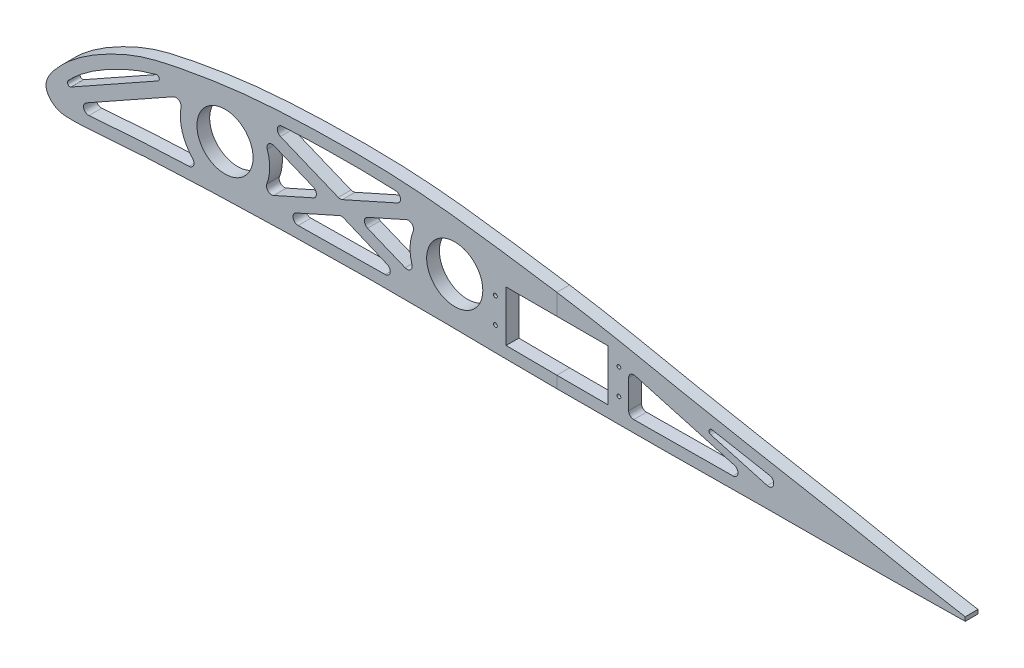
SolidWorks part; units mm, degrees
ref_plane "Front Plane" through (0, 0, 0) normal (0, 0, 1) x (1, 0, 0)
ref_plane "Top Plane" through (0, 0, 0) normal (0, 1, 0) x (1, 0, 0)
ref_plane "Right Plane" through (0, 0, 0) normal (1, 0, 0) x (0, 0, -1)
curve "Curve2"
  spline degree 3 poles (360, 0.774, 0) (353.9747, 1.7923, 0) (341.8992, 3.833, 0) (317.929, 8.8515, 0) (287.8005, 14.3115, 0) (251.6459, 20.8994, 0) (215.7742, 28.6405, 0) (179.6243, 33.9497, 0) (143.6184, 38.7406, 0) (107.4505, 38.9574, 0) (77.3391, 37.3603, 0) (53.4361, 33.3953, 0) (38.2175, 30.219, 0) (26.4469, 25.0774, 0) (17.386, 20.225, 0) (9.7945, 14.7499, 0) (3.5415, 8.6051, 0) (-2.4818, 0.9357, 0) (3.758, -5.4139, 0) (10.5774, -5.7626, 0) (18.0806, -5.3806, 0) (27.0623, -4.6056, 0) (39.0449, -3.7653, 0) (54.0396, -3.0817, 0) (78.026, -2.1616, 0) (108.0193, -1.4806, 0) (144.023, -1.1541, 0) (180.0214, -1.8085, 0) (216.0253, -1.9147, 0) (252.0235, -1.7429, 0) (288.0192, -1.2657, 0) (318.0184, -1.4154, 0) (342.0107, -1.0116, 0) (354.0048, -0.8532, 0) (360, -0.774, 0) knots 0 0 0 0 0.02483 0.049761 0.099505 0.149249 0.199104 0.24856 0.297718 0.346503 0.395331 0.419969 0.445008 0.458171 0.47196 0.48692 0.495371 0.509218 0.518335 0.524512 0.536705 0.548918 0.561125 0.585522 0.609907 0.65867 0.70743 0.756207 0.804971 0.853736 0.902492 0.951256 0.975635 1 1 1 1
sketch "Sketch1" plane through (0, 0, 0) normal (0, 0, 1) x (1, 0, 0)
  line L0 (360, 0.774) -> (360, -0.774)
  spline S0 degree 3 poles (460.5954, -1977.8862) (673.5327, 25.178) (493.5092, -27.9082) (317.929, 8.8515) (287.8005, 14.3115) (251.6459, 20.8994) (215.7742, 28.6405) (179.6243, 33.9497) (143.6184, 38.7406) (107.4505, 38.9574) (77.3391, 37.3603) (53.4361, 33.3953) (38.2175, 30.219) (26.4469, 25.0774) (17.386, 20.225) (9.7945, 14.7499) (3.5415, 8.6051) (-2.4818, 0.9357) (3.758, -5.4139) (10.5774, -5.7626) (18.0806, -5.3806) (27.0623, -4.6056) (39.0449, -3.7653) (54.0396, -3.0817) (78.026, -2.1616) (108.0193, -1.4806) (144.023, -1.1541) (180.0214, -1.8085) (216.0253, -1.9147) (252.0235, -1.7429) (288.0192, -1.2657) (318.0184, -1.4154) (662.5746, 4.3841) (995.4005, -23.4398) (1308.3871, 1672.4433) knots -0.629362 -0.629362 -0.629362 -0.629362 0.02483 0.049761 0.099505 0.149249 0.199104 0.24856 0.297718 0.346503 0.395331 0.419969 0.445008 0.458171 0.47196 0.48692 0.495371 0.509218 0.518335 0.524512 0.536705 0.548918 0.561125 0.585522 0.609907 0.65867 0.70743 0.756207 0.804971 0.853736 0.902492 0.951256 0.975635 2.302817 2.302817 2.302817 2.302817 only from (360, 0.774) to (360, -0.774) construction
  spline S1 degree 3 poles (360, 0.774) (353.9747, 1.7923) (341.8992, 3.833) (317.929, 8.8515) (287.8005, 14.3115) (251.6459, 20.8994) (215.7742, 28.6405) (179.6243, 33.9497) (143.6184, 38.7406) (107.4505, 38.9574) (77.3391, 37.3603) (53.4361, 33.3953) (38.2175, 30.219) (26.4469, 25.0774) (17.386, 20.225) (9.7945, 14.7499) (3.5415, 8.6051) (-2.4818, 0.9357) (3.758, -5.4139) (10.5774, -5.7626) (18.0806, -5.3806) (27.0623, -4.6056) (39.0449, -3.7653) (54.0396, -3.0817) (78.026, -2.1616) (108.0193, -1.4806) (144.023, -1.1541) (180.0214, -1.8085) (216.0253, -1.9147) (252.0235, -1.7429) (288.0192, -1.2657) (318.0184, -1.4154) (342.0107, -1.0116) (354.0048, -0.8532) (360, -0.774) knots 0 0 0 0 0.02483 0.049761 0.099505 0.149249 0.199104 0.24856 0.297718 0.346503 0.395331 0.419969 0.445008 0.458171 0.47196 0.48692 0.495371 0.509218 0.518335 0.524512 0.536705 0.548918 0.561125 0.585522 0.609907 0.65867 0.70743 0.756207 0.804971 0.853736 0.902492 0.951256 0.975635 1 1 1 1
extrude "Boss-Extrude1" add sketch "Sketch1" along normal blind 5
sketch "Sketch3" plane through (0, 0, 5) normal (0, 0, 1) x (1, 0, 0)
  line L0 (284.1512, 10.3055) -> (284.9744, 10.1558)
  line L3 (285, -1.3899) -> (284.9744, 3.21) construction
  line L4 (284.9744, 10.1558) -> (284.9744, 14.8312) construction
  line L5 (284.9744, 3.21) -> (284.9744, 10.1558)
  spline S0 degree 3 poles (344.1847, -2970.9307) (723.5062, 41.4838) (516.074, -32.6324) (317.929, 8.8515) (287.8005, 14.3115) (251.6459, 20.8994) (215.7742, 28.6405) (179.6243, 33.9497) (143.6184, 38.7406) (107.4505, 38.9574) (77.3391, 37.3603) (53.4361, 33.3953) (38.2175, 30.219) (26.4469, 25.0774) (17.386, 20.225) (9.7945, 14.7499) (3.5415, 8.6051) (-2.4818, 0.9357) (3.758, -5.4139) (10.5774, -5.7626) (18.0806, -5.3806) (27.0623, -4.6056) (39.0449, -3.7653) (54.0396, -3.0817) (78.026, -2.1616) (108.0193, -1.4806) (144.023, -1.1541) (180.0214, -1.8085) (216.0253, -1.9147) (252.0235, -1.7429) (288.0192, -1.2657) (318.0184, -1.4154) (716.4553, 5.2911) (1103.2559, -33.3331) (1462.1178, 2660.5017) knots -0.723033 -0.723033 -0.723033 -0.723033 0.02483 0.049761 0.099505 0.149249 0.199104 0.24856 0.297718 0.346503 0.395331 0.419969 0.445008 0.458171 0.47196 0.48692 0.495371 0.509218 0.518335 0.524512 0.536705 0.548918 0.561125 0.585522 0.609907 0.65867 0.70743 0.756207 0.804971 0.853736 0.902492 0.951256 0.975635 2.521796 2.521796 2.521796 2.521796 only from (360, 0.774) to (360, -0.774) construction
  spline S1 degree 3 poles (284.9744, 14.8312) (273.8733, 16.8505) (250.7091, 21.1015) (215.7742, 28.6405) (179.6243, 33.9497) (143.6184, 38.7406) (107.4505, 38.9574) (77.3391, 37.3603) (53.4361, 33.3953) (38.2175, 30.219) (26.4469, 25.0774) (17.386, 20.225) (9.7945, 14.7499) (3.5415, 8.6051) (-2.4818, 0.9357) (3.758, -5.4139) (10.5774, -5.7626) (18.0806, -5.3806) (27.0623, -4.6056) (39.0449, -3.7653) (54.0396, -3.0817) (78.026, -2.1616) (108.0193, -1.4806) (144.023, -1.1541) (180.0214, -1.8085) (216.0253, -1.9147) (251.0175, -1.7477) (274.0081, -1.4511) (285, -1.3899) knots 0.103398 0.103398 0.103398 0.103398 0.149249 0.199104 0.24856 0.297718 0.346503 0.395331 0.419969 0.445008 0.458171 0.47196 0.48692 0.495371 0.509218 0.518335 0.524512 0.536705 0.548918 0.561125 0.585522 0.609907 0.65867 0.70743 0.756207 0.804971 0.853736 0.898404 0.898404 0.898404 0.898404 construction
  spline S2 degree 1 poles (284.1512, 10.3055) (284.9744, 3.21) knots 0 0 1 1 construction
  spline S3 degree 3 poles (284.1512, 10.3055) (278.1277, 11.4011) (266.0952, 13.5977) (248.0033, 17.0941) (230.0297, 20.8366) (212.1625, 24.3023) (194.1819, 27.1662) (176.0385, 29.7488) (157.941, 32.1627) (139.9629, 33.7938) (121.8825, 34.2715) (103.6458, 33.9966) (88.5285, 33.2788) (76.5491, 32.181) (67.6356, 31.0449) (58.7258, 29.5821) (49.758, 27.9291) (42.5828, 26.2693) (37.1269, 24.5364) (33.1259, 22.9657) (29.1255, 21.1456) (25.1876, 19.172) (21.3948, 17.0517) (17.7124, 14.7189) (14.2021, 12.1748) (11.0304, 9.5132) (8.6387, 7.1256) (6.5778, 4.8171) (5.3253, 3.1689) (4.5747, 1.7655) (4.4647, 1.1378) (4.4812, 1.0445) (4.4784, 1.0061) (4.8205, 0.3506) (5.6085, -0.325) (6.2267, -0.6574) (6.7532, -0.8463) (7.8538, -1.0238) (10.0098, -1.0519) (12.1694, -1.0299) (14.3579, -0.9469) (16.5714, -0.8217) (19.5647, -0.6155) (23.3403, -0.3137) (27.9445, 0.059) (32.5568, 0.3895) (38.7092, 0.7806) (46.3902, 1.1764) (55.5744, 1.5696) (67.8164, 2.053) (83.1362, 2.5431) (107.6344, 3.0806) (132.1396, 3.3831) (156.6801, 3.1986) (175.0192, 2.9224) (193.3182, 2.7563) (217.7439, 2.7049) (242.175, 2.7972) (266.6035, 3.0568) (278.8536, 3.176) (284.9744, 3.21) knots 0.103398 0.103398 0.103398 0.103398 0.128242 0.153086 0.17793 0.202774 0.227618 0.252461 0.277305 0.302149 0.326993 0.351837 0.376681 0.389103 0.401525 0.413947 0.426369 0.438791 0.445002 0.451213 0.457424 0.463635 0.469846 0.476057 0.482268 0.488479 0.49469 0.497795 0.500901 0.504006 0.507112 0.508664 0.510217 0.513323 0.516428 0.517981 0.519534 0.522639 0.525745 0.52885 0.531956 0.535061 0.538167 0.544378 0.550589 0.5568 0.563011 0.575433 0.587855 0.600276 0.62512 0.649964 0.699652 0.724496 0.74934 0.774184 0.799028 0.848716 0.87356 0.898404 0.898404 0.898404 0.898404
  point P6 (284.1454, 10.3065)
  point P8 (284.9744, 10.1558)
  point P9 (283.0131, 3.1981)
  point P10 (-44.9663, 74.673)
  point P11 (254.7158, 9.2251)
  dimension "D1" = 284.9744
  dimension "D2" = 4.6
extrude "Cut-Extrude2" cut sketch "Sketch3" against normal blind 10
sketch "Sketch4" plane through (0, 0, 5) normal (0, 0, 1) x (1, 0, 0)
  circle A0 centre (70, 17) radius 11
  circle A1 centre (160, 17) radius 11
  circle A2 centre (70, 17) radius 17.5
  circle A3 centre (160, 17) radius 17.5
  point P7 (0, 0)
  point P9 (174.8211, 11.0215)
  dimension "D1" = 22
  dimension "D2" = 35
  dimension "D3" = 17
  dimension "D4" = 70
  dimension "D5" = 90
  dimension "D6" = 0
extrude "Boss-Extrude2" add sketch "Sketch4" against normal up to surface (5 mm away) up to face at (284.5628, 9.073, 0)
sketch "Sketch7" plane through (0, 0, 5) normal (0, 0, 1) x (1, 0, 0)
  line L0 (220.125, 22.7363) -> (220.125, 2.7363)
  line L1 (220.125, 2.7363) -> (228.125, 2.7572)
  line L2 (228.125, 2.7572) -> (228.125, 21.1756)
  line L3 (228.125, 21.1756) -> (220.125, 22.7363)
  spline S0 degree 3 poles (284.1512, 10.3055) (278.1277, 11.4011) (266.0952, 13.5977) (248.0033, 17.0941) (230.0297, 20.8366) (212.1625, 24.3023) (194.1819, 27.1662) (180.4993, 29.1138) (172.8767, 30.1558) (171.293, 30.3686) knots 0.103398 0.103398 0.103398 0.103398 0.128242 0.153086 0.17793 0.202774 0.227618 0.252461 0.258981 0.258981 0.258981 0.258981 construction
  spline S2 degree 3 poles (170.4973, 2.9979) (172.0028, 2.9782) (179.6158, 2.8806) (193.3182, 2.7563) (217.7439, 2.7049) (242.175, 2.7972) (266.6035, 3.0568) (278.8536, 3.176) (284.9744, 3.21) knots 0.743218 0.743218 0.743218 0.743218 0.74934 0.774184 0.799028 0.848716 0.87356 0.898404 0.898404 0.898404 0.898404 construction
  point P4 (0, 0)
  point P8 (0, 0)
  point P9 (0, 0)
  point P11 (0, 0)
  dimension "D1" = 20
  dimension "D2" = 8
extrude "Boss-Extrude3" add sketch "Sketch7" against normal up to surface (5 mm away) separate body up to face at (115.4745, 17.8841, 0)
sketch "Sketch8" plane through (0, 0, 5) normal (0, 0, 1) x (1, 0, 0)
  line L0 (220.125, 22.7363) -> (180.125, 22.7363)
  line L1 (180.125, 22.7363) -> (180.125, 2.8833)
  line L2 (180.125, 2.8833) -> (170.4973, 2.9979)
  arc A0 (170.4973, 2.9979) -> (171.293, 30.3686) centre (160, 17) ccw construction
  arc A1 (170.4973, 2.9979) -> (171.293, 30.3686) centre (160, 17) ccw
  spline S0 degree 3 poles (284.9744, 3.21) (278.8536, 3.176) (266.6035, 3.0568) (242.175, 2.7972) (217.7439, 2.7049) (193.3182, 2.7563) (179.6158, 2.8806) (172.0028, 2.9782) (170.4973, 2.9979) knots 0.743218 0.743218 0.743218 0.743218 0.768062 0.792906 0.842594 0.867438 0.892282 0.898404 0.898404 0.898404 0.898404 construction
  spline S2 degree 3 poles (1592.2153, -1477.288) (696.0261, -24.2566) (480.0708, -27.7549) (248.0033, 17.0941) (230.0297, 20.8366) (212.1625, 24.3023) (194.1819, 27.1662) (19.9409, 51.968) (-142.3404, 54.1761) (-56.8689, -1936.9544) knots -0.778101 -0.778101 -0.778101 -0.778101 0.128242 0.153086 0.17793 0.202774 0.227618 0.252461 0.918543 0.918543 0.918543 0.918543 only from (284.1512, 10.3055) to (171.293, 30.3686) construction
  spline S3 degree 3 poles (220.125, 22.7363) (217.4662, 23.2416) (208.8406, 24.8314) (194.1819, 27.1662) (180.4993, 29.1138) (172.8767, 30.1558) (171.293, 30.3686) knots 0.1917 0.1917 0.1917 0.1917 0.202774 0.227618 0.252461 0.258981 0.258981 0.258981 0.258981
  point P3 (174.4931, 29.9341)
  point P10 (0, 0)
  point P11 (0, 0)
  point P14 (0, 0)
  dimension "D3" = 40
extrude "Boss-Extrude4" add sketch "Sketch8" against normal up to surface (5 mm away) separate body up to face at (115.4745, 17.8841, 0)
sketch "Sketch12" plane through (0, 0, 5) normal (0, 0, 1) x (1, 0, 0)
  line L0 (78.444, 32.328) -> (149.1779, 3.2474) construction
  line L1 (152.1517, 32.6414) -> (79.6719, 2.4156) construction
  line L2 (79.3946, 34.6403) -> (115.1661, 19.9336)
  line L3 (5.2509, 0) -> (57.607, 29.3557) construction
  line L4 (79.3946, 34.6403) -> (77.4934, 30.0158)
  line L5 (150.1285, 5.5597) -> (148.2273, 0.9352)
  line L6 (77.4934, 30.0158) -> (108.8675, 17.1171)
  line L7 (79.3946, 34.6403) -> (148.2273, 0.9352) construction
  line L8 (150.1285, 5.5597) -> (77.4934, 30.0158) construction
  line L9 (150.7357, 35.8392) -> (115.1661, 19.9336)
  line L10 (150.7357, 35.8392) -> (152.7767, 31.2748)
  line L11 (79.0469, 3.7823) -> (81.088, -0.7821)
  line L12 (152.7767, 31.2748) -> (121.5475, 17.3101)
  line L13 (150.7357, 35.8392) -> (81.088, -0.7821) construction
  line L14 (79.0469, 3.7823) -> (152.7767, 31.2748) construction
  line L15 (108.8675, 17.1171) -> (79.0469, 3.7823)
  line L18 (115.6434, 14.6699) -> (148.2273, 0.9352)
  line L19 (115.6434, 14.6699) -> (81.088, -0.7821)
  line L21 (121.5475, 17.3101) -> (150.1285, 5.5597)
  line L23 (4.0282, 2.1806) -> (56.3843, 31.5363)
  line L25 (56.3843, 31.5363) -> (58.8296, 27.175)
  line L26 (6.4735, -2.1806) -> (58.8296, 27.175)
  line L27 (4.0282, 2.1806) -> (58.8296, 27.175) construction
  line L28 (56.3843, 31.5363) -> (6.4735, -2.1806) construction
  line L29 (4.0282, 2.1806) -> (4.0282, -2.1806)
  line L30 (4.0282, -2.1806) -> (6.4735, -2.1806)
  spline S1 degree 3 poles (57.607, 29.3557) (54.9958, 28.8936) (49.4019, 27.8467) (42.5828, 26.2693) (37.1269, 24.5364) (33.1259, 22.9657) (29.1255, 21.1456) (25.1876, 19.172) (21.3948, 17.0517) (17.7124, 14.7189) (14.2021, 12.1748) (11.0304, 9.5132) (8.6387, 7.1256) (6.5778, 4.8171) (5.3253, 3.1689) (4.5747, 1.7655) (4.4647, 1.1378) (4.4812, 1.0445) (4.4784, 1.0061) (4.8205, 0.3506) (5.6085, -0.325) (6.2267, -0.6574) (6.7532, -0.8463) (7.8538, -1.0238) (10.0098, -1.0519) (12.1694, -1.0299) (14.3579, -0.9469) (16.5714, -0.8217) (19.5647, -0.6155) (23.3403, -0.3137) (27.9445, 0.059) (32.5568, 0.3895) (38.7092, 0.7806) (46.3902, 1.1764) (54.4341, 1.5208) (59.4155, 1.7206) (61.3364, 1.795) knots 0.415488 0.415488 0.415488 0.415488 0.426369 0.438791 0.445002 0.451213 0.457424 0.463635 0.469846 0.476057 0.482268 0.488479 0.49469 0.497795 0.500901 0.504006 0.507112 0.508664 0.510217 0.513323 0.516428 0.517981 0.519534 0.522639 0.525745 0.52885 0.531956 0.535061 0.538167 0.544378 0.550589 0.5568 0.563011 0.575433 0.587855 0.59565 0.59565 0.59565 0.59565 construction
  point P9 (113.811, 17.7877)
  point P11 (115.9118, 17.5285)
  point P14 (31.4289, 14.6778)
  point P18 (113.811, 17.7877)
  point P24 (115.9118, 17.5285)
  point P25 (31.4289, 14.6778)
  dimension "D1" = 5
  dimension "D2" = 5
  dimension "D3" = 5
  dimension "D4" = 5
extrude "Boss-Extrude9" add sketch "Sketch12" against normal blind 5
fillet "Fillet2" radius 2 16 edges at (61.3364, 1.795, 2.5) (54.2362, 24.5996, 2.5) (8.5414, -1.0212, 2.5) (108.8675, 17.1171, 2.5) (84.1685, 27.2715, 2.5) (83.3791, 5.7195, 2.5) (88.7768, 2.6561, 2.5) (115.6434, 14.6699, 2.5) (142.6509, 3.2858, 2.5) (115.1661, 19.9336, 2.5) (83.8148, 32.823, 2.5) (121.5475, 17.3101, 2.5) (145.265, 7.5592, 2.5) (146.9643, 28.6756, 2.5) (144.9759, 33.2636, 2.5) (284.9744, 10.1558, 2.5)
fillet "Fillet3" radius 1 2 edges at (49.8693, 27.8834, 2.5) (5.1623, 2.8165, 2.5)
sketch "Sketch13" plane through (0, 0, 5) normal (0, 0, 1) x (1, 0, 0)
  line L0 (180.125, 10.6) -> (180.125, 1.0479)
  line L1 (180.125, 2.8833) -> (180.125, 22.7363) construction
  line L2 (180.125, 1.0479) -> (168.104, 1.4166)
  line L3 (168.104, 1.4166) -> (171.8913, 7.7846)
  line L4 (171.8913, 7.7846) -> (174.7292, 21.2752)
  line L5 (174.7292, 21.2752) -> (168.9346, 28.4996)
  line L6 (168.9346, 28.4996) -> (169.8276, 32.7447)
  line L7 (169.8276, 32.7447) -> (180.125, 30.5785)
  line L8 (180.125, 30.5785) -> (180.125, 10.6)
extrude "Boss-Extrude10" add sketch "Sketch13" against normal blind 5
sketch "Sketch14" plane through (0, 0, 5) normal (0, 0, 1) x (1, 0, 0)
  line L0 (220.125, 22.7363) -> (220.125, 1.2947)
  line L10 (220.125, 22.7363) -> (228.125, 22.7363)
  line L11 (220.125, 1.2947) -> (228.125, 1.2947)
  line L12 (228.125, 22.7363) -> (228.125, 1.2947)
  line L13 (228.125, 2.7572) -> (228.125, 21.1756) construction
extrude "Boss-Extrude11" add sketch "Sketch14" against normal blind 5
fillet "Fillet4" radius 2 1 edges at (228.125, 2.7572, 2.5)
sketch "Sketch15" plane through (0, 0, 5) normal (0, 0, 1) x (1, 0, 0)
  line L0 (228.125, 21.1756) -> (284.9744, 3.21) construction
  line L1 (227.437, 18.777) -> (284.8544, 2.7195)
  line L2 (227.437, 18.777) -> (228.245, 21.6661)
  line L3 (284.8544, 2.7195) -> (285.6624, 5.6086)
  line L4 (228.245, 21.6661) -> (285.6624, 5.6086)
  line L5 (227.437, 18.777) -> (285.6624, 5.6086) construction
  line L6 (284.8544, 2.7195) -> (228.245, 21.6661) construction
  point P4 (0, 0)
  point P5 (256.5497, 12.1928)
  point P6 (256.5497, 12.1928)
  dimension "D1" = 3
extrude "Boss-Extrude12" add sketch "Sketch15" against normal blind 5
fillet "Fillet5" radius 2 3 edges at (284.9744, 5.801, 2.5) (283.1394, 3.1991, 2.5) (228.125, 18.5846, 2.5)
fillet "Fillet6" radius 1 1 edges at (234.8742, 19.8122, 2.5)
sketch "Sketch16" plane through (0, 0, 5) normal (0, 0, 1) x (1, 0, 0)
  line L0 (220.125, 22.7363) -> (220.125, 2.7363) construction
  line L1 (180.125, 22.7363) -> (220.125, 22.7363) construction
  line L2 (200.125, 41.7942) -> (200.125, -10.8295) construction
  line L3 (180.125, 2.8833) -> (180.125, 22.7363) construction
  circle A0 centre (224.325, 17.7363) radius 0.75
  circle A1 centre (224.325, 7.7363) radius 0.75
  circle A2 centre (175.925, 17.7363) radius 0.75
  circle A3 centre (175.925, 7.7363) radius 0.75
  point P14 (0, 0)
  point P15 (0, 0)
  point P16 (0, 0)
  point P17 (0, 0)
  dimension "D4" = 1.5
  dimension "D6" = 1.5
  dimension "D1" = 10
  dimension "D2" = 4.2
  dimension "D3" = 5
  dimension "D5" = 20
  dimension "D7" = 4.2
extrude "Cut-Extrude4" cut sketch "Sketch16" against normal through all both and the other way through all
ref_plane "Plane2" through (200, 0, 0) normal (1, 0, 0) x (0, 0, -1)
split "Split1" trim tools "Plane2" bodies to split 116 resulting bodies 117 118
